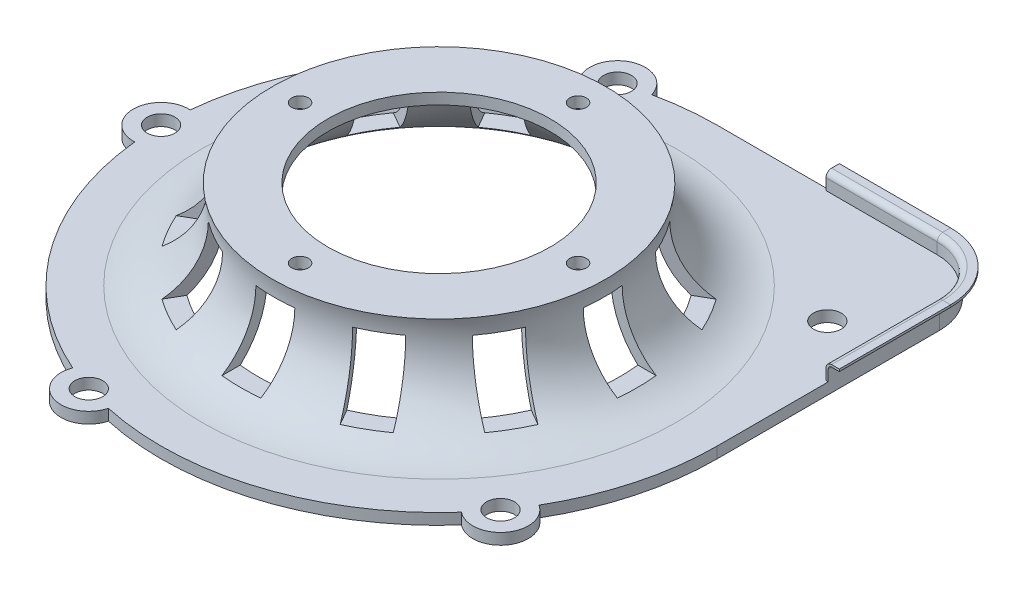
SolidWorks part; units mm, degrees
material "Alloy Steel"
ref_plane "Front Plane" through (0, 0, 0) normal (0, 0, 1) x (1, 0, 0)
ref_plane "Top Plane" through (0, 0, 0) normal (0, 1, 0) x (1, 0, 0)
ref_plane "Right Plane" through (0, 0, 0) normal (1, 0, 0) x (0, 0, -1)
sketch "Sketch1" plane through (0, 0, 0) normal (0, 0, 1) x (1, 0, 0)
  line L0 (0, 63.7682) -> (0, -63.7682) construction
  line L1 (100, 90) -> (100, 80)
  line L2 (100, 80) -> (138.4124, 80)
  line L3 (213.2456, 0) -> (250, 0)
  line L4 (250, 0) -> (250, 10)
  line L5 (100, 90) -> (150, 90)
  line L6 (213.2456, 10) -> (250, 10)
  arc A0 (138.4124, 80) -> (213.2456, 0) centre (213.2456, 75) ccw
  arc A1 (150, 90) -> (213.2456, 10) centre (213.2456, 75) ccw
  point P4 (0, 0)
  dimension "D4" = 65
  dimension "D2" = 200
  dimension "D3" = 300
  dimension "D5" = 500
  dimension "D6" = 80
  dimension "D1" = 10
revolve "Revolve1" add sketch "Sketch1" angle 360 about L0
sketch "Sketch3" plane through (0, 0, 0) normal (0, -1, 0) x (1, 0, 0)
  line L4 (250, -200) -> (250, 0)
  line L5 (200, -250) -> (0, -250)
  arc A4 (0, -250) -> (250, 0) centre (0, 0) ccw
  circle A5 centre (0, 0) radius 250 construction
  arc A7 (-248.75, 24.9687) -> (-248.75, -24.9687) centre (-250, 0) ccw
  arc A8 (-248.75, 24.9687) -> (-248.75, -24.9687) centre (0, 0) ccw
  arc A9 (-53.1213, 244.2911) -> (-100.6147, 228.8595) centre (-77.2542, 237.7641) ccw
  arc A10 (-53.1213, 244.2911) -> (-100.6147, 228.8595) centre (0, 0) ccw
  arc A11 (215.9192, 126.0115) -> (186.5667, 166.4117) centre (202.2542, 146.9463) ccw
  arc A12 (215.9192, 126.0115) -> (186.5667, 166.4117) centre (0, 0) ccw
  arc A13 (186.5667, -166.4117) -> (215.9192, -126.0115) centre (202.2542, -146.9463) ccw [skipped]
  arc A14 (186.5667, -166.4117) -> (215.9192, -126.0115) centre (0, 0) ccw [skipped]
  arc A15 (-100.6147, -228.8595) -> (-53.1213, -244.2911) centre (-77.2542, -237.7641) ccw
  arc A16 (-100.6147, -228.8595) -> (-53.1213, -244.2911) centre (0, 0) ccw
  arc A17 (250, -200) -> (200, -250) centre (200, -200) cw
  point P26 (0, 0)
  dimension "D1" = 50
  dimension "D3" = 50
  dimension "D2" = 5
extrude "Boss-Extrude1" add sketch "Sketch3" against normal blind 10
ref_plane "Plane2" through (0, 70, 0) normal (0, 1, 0) x (1, 0, 0)
sketch "Sketch6" plane through (0, 0, 0) normal (0, 0, -1) x (-1, 0, 0)
  line L0 (0, 0) -> (0, 165.3024) construction
  line L1 (-17.5, 75) -> (17.5, 75)
  line L2 (-17.5, 75) -> (-17.5, 20)
  line L3 (-17.5, 20) -> (17.5, 20)
  line L4 (17.5, 75) -> (17.5, 20)
  dimension "D1" = 35
  dimension "D2" = 55
  dimension "D4" = 20
extrude "Cut-Extrude2" cut sketch "Sketch6" along normal up to next
pattern_circular "CirPattern1" count 11 every 30 about axis through (0, 0, 0) along (0, 1, 0) of "Cut-Extrude2"
sketch "Sketch8" plane through (0, 90, 0) normal (0, 1, 0) x (1, 0, 0)
  line L0 (0, 0) -> (0, 140.6621) construction
  circle A4 centre (0, 125) radius 7.5
  circle A5 centre (125, 0) radius 7.5
  circle A6 centre (0, -125) radius 7.5
  circle A7 centre (-125, 0) radius 7.5
  point P13 (0, 0)
  dimension "D2" = 125
  dimension "D1" = 15
extrude "Cut-Extrude4" cut sketch "Sketch8" against normal up to surface (10 mm away) up to face at (0, 80, 138.4124)
sketch "Sketch9" plane through (0, 10, 0) normal (0, 1, 0) x (1, 0, 0)
  circle A0 centre (-77.2542, 237.7641) radius 12.5
  circle A7 centre (202.2542, 146.9463) radius 12.5
  circle A8 centre (202.2542, -146.9463) radius 12.5
  circle A9 centre (-77.2542, -237.7641) radius 12.5
  circle A10 centre (-250, 0) radius 12.5
  circle A11 centre (0, 0) radius 100 construction
  point P16 (0, 0)
  dimension "D1" = 25
  dimension "D2" = 5
extrude "Cut-Extrude5" cut sketch "Sketch9" against normal up to next
ref_plane "Plane1" through (0, 0, -100) normal (0, 0, 1) x (1, 0, 0)
sketch "Sketch10" plane through (0, 0, -100) normal (0, 0, -1) x (-1, 0, 0)
  line L12 (-200, 10) -> (-250, 10) construction
  line L14 (-253, 23) -> (-260, 23)
  line L15 (-250, 20) -> (-250, 10)
  line L16 (-250, 10) -> (-248, 10)
  line L17 (-248, 20) -> (-248, 10)
  line L18 (-260, 25) -> (-260, 23)
  line L19 (-253, 25) -> (-260, 25)
  arc A3 (-250, 20) -> (-253, 23) centre (-253, 20) ccw
  arc A4 (-248, 20) -> (-253, 25) centre (-253, 20) ccw
  dimension "D2" = 5
  dimension "D1" = 2
  dimension "D3" = 2
  dimension "D4" = 10
  dimension "D5" = 10
sketch "Sketch11" plane through (0, 10, 0) normal (0, 1, 0) x (1, 0, 0)
  line L0 (250, 200) -> (250, 100)
  line L4 (200, 250) -> (100, 250)
  arc A0 (250, 200) -> (200, 250) centre (200, 200) ccw construction
  arc A1 (250, 200) -> (200, 250) centre (200, 200) ccw
  dimension "D1" = 100
sweep "Sweep1" add profiles "Sketch10" path "Sketch11"
